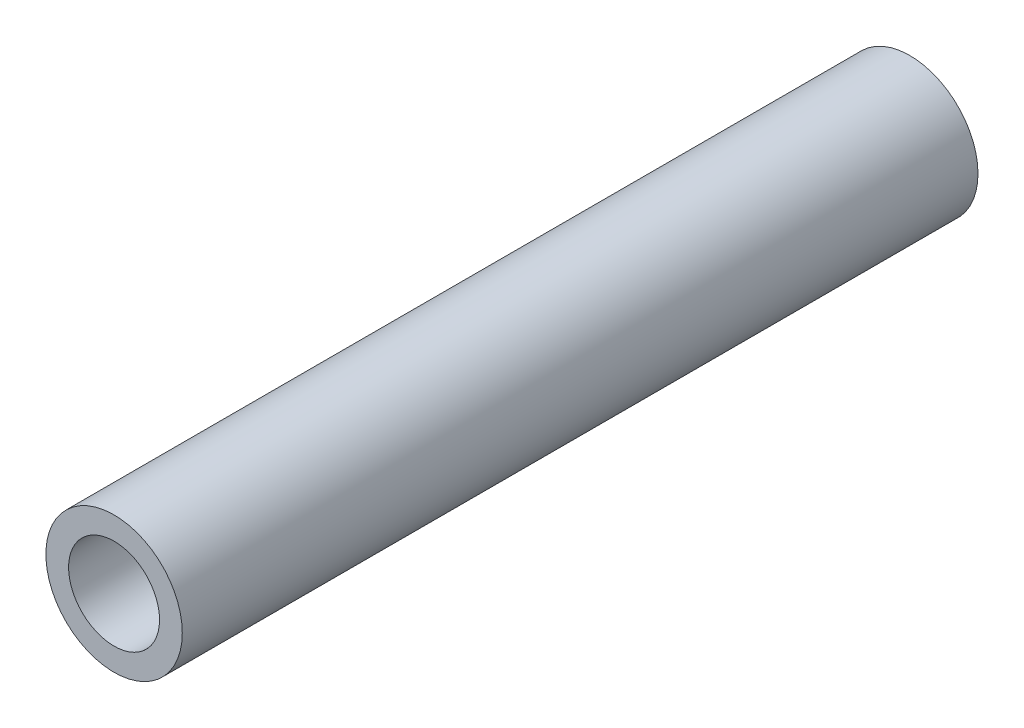
SolidWorks part; units mm, degrees
ref_plane "前视基准面" through (0, 0, 0) normal (0, 0, 1) x (1, 0, 0)
ref_plane "上视基准面" through (0, 0, 0) normal (0, 1, 0) x (1, 0, 0)
ref_plane "右视基准面" through (0, 0, 0) normal (1, 0, 0) x (0, 0, -1)
sketch "草图1" plane through (0, 0, 0) normal (0, 0, 1) x (1, 0, 0)
  circle A0 centre (0, 0) radius 3
  circle A1 centre (0, 0) radius 2
  dimension "D1" = 4
  dimension "D2" = 6
extrude "凸台-拉伸1" add sketch "草图1" along normal mid plane 35
